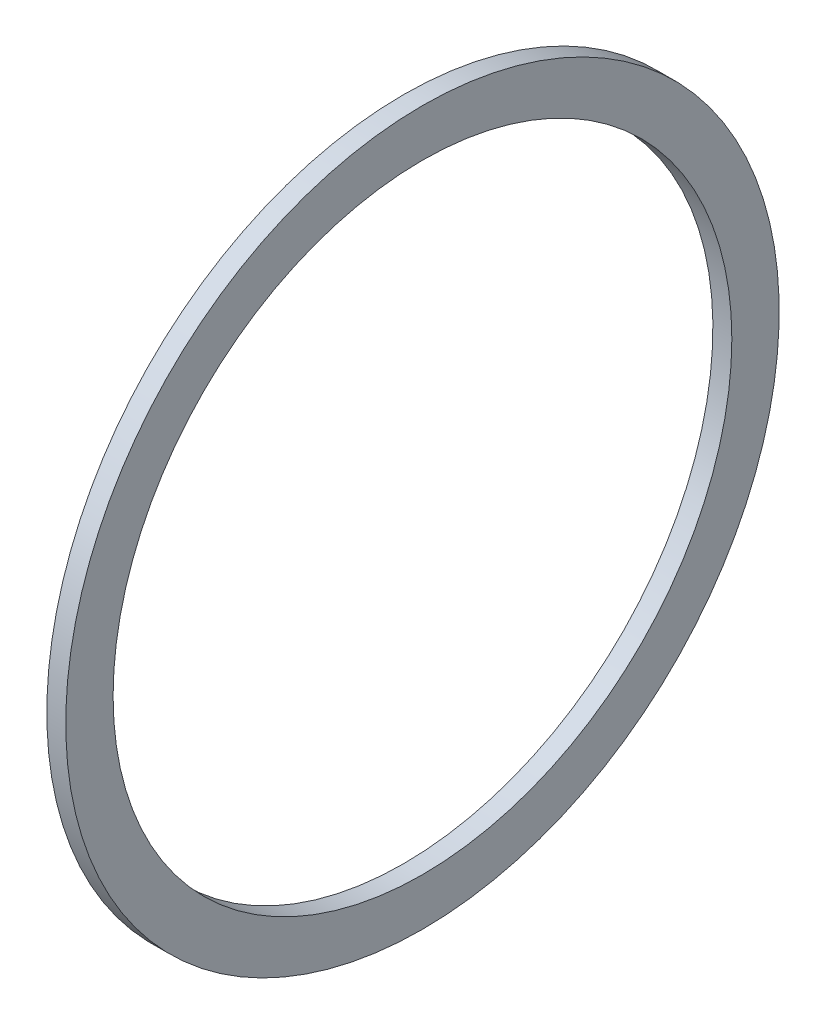
SolidWorks part; units mm, degrees
material "Polyurethane Foam Flexible"
ref_plane "Ebene vorne" through (0, 0, 0) normal (0, 0, 1) x (1, 0, 0)
ref_plane "Ebene oben" through (0, 0, 0) normal (0, 1, 0) x (1, 0, 0)
ref_plane "Ebene rechts" through (0, 0, 0) normal (1, 0, 0) x (0, 0, -1)
sketch "Skizze1" plane through (0, 0, 0) normal (0, 0, 1) x (1, 0, 0)
  line L0 (-38.0534, 66.25) -> (-41.0534, 66.25)
  line L2 (-41.0534, 13.3) -> (-38.0534, 13.3)
  line L5 (-41.0534, 13.3) -> (-41.0534, 66.25)
  line L8 (-17.6629, 9.75) -> (-37.0534, 9.75) construction
  line L12 (-38.0534, 13.3) -> (-38.0534, 66.25)
  line L25 (-41.0534, 28.75) -> (-41.0534, 26.8663) construction
  dimension "D5" = 113
  dimension "D2" = 7.1
  dimension "D6" = 3
revolve "Rotation1" add sketch "Skizze1" angle 360 about L8
hole_wizard "Ø4.7 (4.7) Durchmesser Bohrung1" positions "Skizze3" profile "Skizze4" hole size "Ø4.7" standard "DIN" end condition through all
sketch "Skizze3" plane through (-41.0534, 11.9687, 19.8689) normal (-1, 0, 0) x (0, 0, 1)
  point P0 (-13.505, -8.5827)
  point P3 (-26.2329, -8.5827)
  point P6 (-26.2329, 4.1452)
  point P9 (-13.505, 4.1452)
sketch "Skizze4" plane through (-41.0534, 3.386, 6.364) normal (0, 1, 0) x (0, 0, 1)
  line L0 (0, 0) -> (0, 3)
  line L1 (0, 3) -> (2.35, 3)
  line L2 (2.35, 3) -> (2.35, 0)
  line L5 (2.35, 0) -> (0, 0)
  line L11 (0, -6.35) -> (0, 107.95) construction
  dimension "Bohrerdurchmesser" = 4.7
  dimension "Bohrungstiefe" = 3
sketch "Skizze5" plane through (-38.0534, 0, 0) normal (1, 0, 0) x (0, 0, -1)
  line L0 (-15.9451, 25.6246) -> (-23.0273, 32.6845) construction
  line L1 (6.364, 3.386) -> (-6.2453, 15.9555) construction
  circle A0 centre (0, 9.75) radius 22.5 construction
  ellipse E0 centre (-23.0273, 32.6845) end of major axis (-5.3776, 50.3901) minor radius 10
  dimension "D1" = 45
  dimension "D3" = 50
  dimension "D4" = 20
extrude "Schnitt-Linear austragen1" cut sketch "Skizze5" against normal up to next (3 mm away)
pattern_circular "Kreismuster1" count 4 over 360 of "Schnitt-Linear austragen1"
ref_plane "Plane1" through (-41.0534, 0, 0) normal (-1, 0, 0) x (0, 0, 1)
sketch "Sketch1" plane through (-41.0534, 0, 0) normal (-1, 0, 0) x (0, 0, 1)
  circle A0 centre (0, 9.75) radius 49
  dimension "D1" = 98
extrude "Cut-Extrude1" cut sketch "Sketch1" against normal up to next
